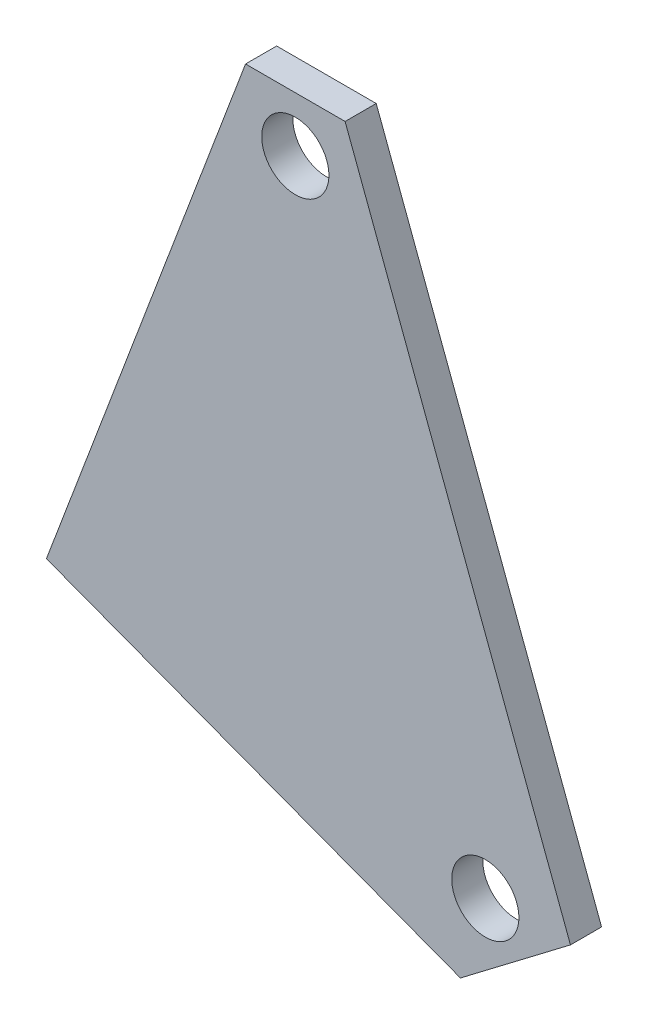
SolidWorks part; units mm, degrees
ref_plane "Front Plane" through (0, 0, 0) normal (0, 0, 1) x (1, 0, 0)
ref_plane "Top Plane" through (0, 0, 0) normal (0, 1, 0) x (1, 0, 0)
ref_plane "Right Plane" through (0, 0, 0) normal (1, 0, 0) x (0, 0, -1)
sketch "Sketch1" plane through (0, 0, 117.7854) normal (0, 0, 1) x (1, 0, 0)
  line L0 (54.1785, 19.6069) -> (42.9492, 11.0692) construction
  line L1 (42.9492, 11.0692) -> (0.6995, 27.0019) construction
  line L2 (0.6995, 27.0019) -> (21.0195, 80.8855) construction
  line L3 (21.0195, 80.8855) -> (31.1795, 80.8855) construction
  line L4 (31.1795, 80.8855) -> (54.1785, 19.6069) construction
  line L5 (54.1785, 19.6069) -> (42.9492, 11.0692)
  line L6 (42.9492, 11.0692) -> (0.6995, 27.0019)
  line L7 (0.6995, 27.0019) -> (21.0195, 80.8855)
  line L8 (21.0195, 80.8855) -> (31.1795, 80.8855)
  line L9 (31.1795, 80.8855) -> (54.1785, 19.6069)
  circle A0 centre (45.4892, 19.3819) radius 3.429 construction
  circle A1 centre (26.0995, 75.2975) radius 3.429 construction
  circle A2 centre (45.4892, 19.3819) radius 3.429
  circle A3 centre (26.0995, 75.2975) radius 3.429
extrude "Boss-Extrude1" add sketch "Sketch1" along normal blind 3.175
